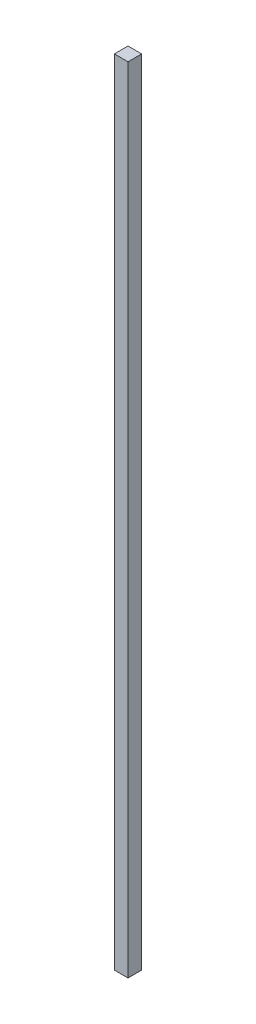
SolidWorks part; units mm, degrees
ref_plane "Front Plane" through (0, 0, 0) normal (0, 0, 1) x (1, 0, 0)
ref_plane "Top Plane" through (0, 0, 0) normal (0, 1, 0) x (1, 0, 0)
ref_plane "Right Plane" through (0, 0, 0) normal (1, 0, 0) x (0, 0, -1)
sketch "Sketch1" plane through (0, 0, 0) normal (0, 1, 0) x (1, 0, 0)
  line L1 (0, 0) -> (25.4, 0)
  line L2 (0, 0) -> (0, 25.4)
  line L3 (0, 25.4) -> (25.4, 25.4)
  line L4 (25.4, 0) -> (25.4, 25.4)
  dimension "D1" = 25.4
  dimension "D2" = 25.4
extrude "Boss-Extrude1" add sketch "Sketch1" along normal blind 1473.2
